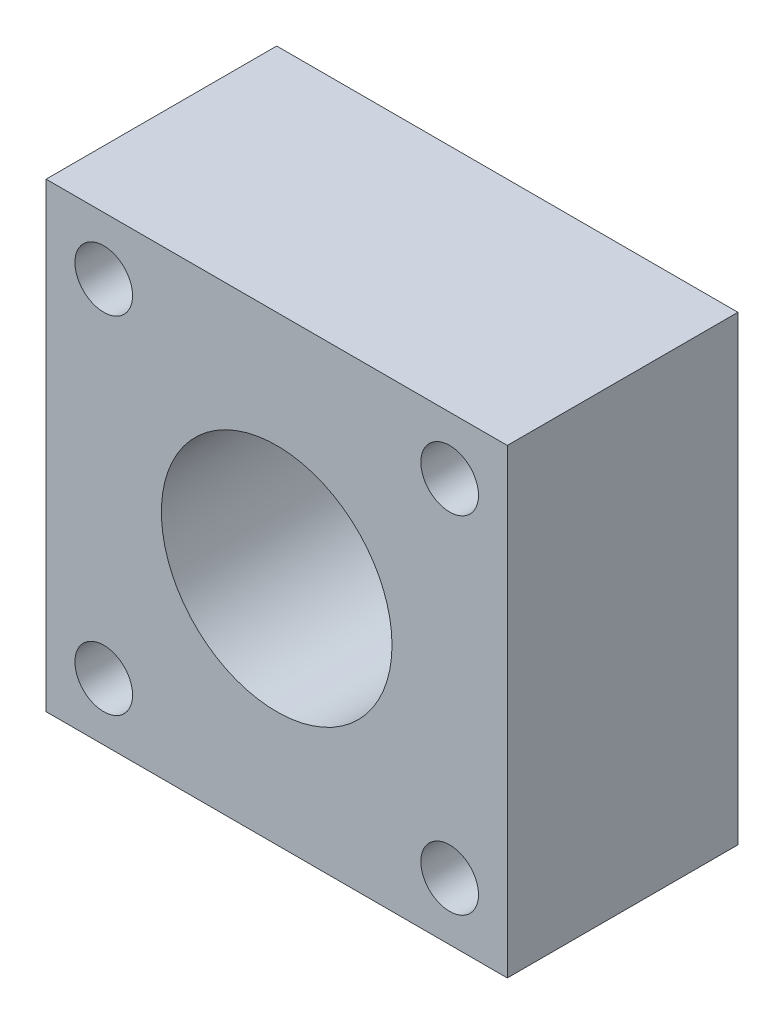
SolidWorks part; units mm, degrees
ref_plane "Front Plane" through (0, 0, 0) normal (0, 0, 1) x (1, 0, 0)
ref_plane "Top Plane" through (0, 0, 0) normal (0, 1, 0) x (1, 0, 0)
ref_plane "Right Plane" through (0, 0, 0) normal (1, 0, 0) x (0, 0, -1)
sketch "Sketch4" plane through (0, 0, 0) normal (0, 0, 1) x (1, 0, 0)
  line L1 (-25.4, 25.4) -> (25.4, 25.4)
  line L2 (-25.4, 25.4) -> (-25.4, -25.4)
  line L3 (-25.4, -25.4) -> (25.4, -25.4)
  line L4 (25.4, 25.4) -> (25.4, -25.4)
  line L5 (-25.4, 25.4) -> (25.4, -25.4) construction
  line L6 (-25.4, -25.4) -> (25.4, 25.4) construction
  point P0 (0, 0)
  dimension "D1" = 50.8
  dimension "D2" = 50.8
extrude "Boss-Extrude2" add sketch "Sketch4" along normal blind 25.4
sketch "Sketch5" plane through (0, 0, 25.4) normal (0, 0, 1) x (1, 0, 0)
  line L0 (25.4, -25.4) -> (25.4, 25.4) construction
  line L1 (25.4, 25.4) -> (-25.4, 25.4) construction
  line L2 (0, 27.1283) -> (0, -35.2779) construction
  circle A0 centre (19.05, 19.05) radius 3.175
  circle A1 centre (0, 0) radius 12.7
  circle A2 centre (-19.05, 19.05) radius 3.175
  circle A3 centre (19.05, -19.05) radius 3.175
  circle A4 centre (-19.05, -19.05) radius 3.175
  dimension "D1" = 6.35
  dimension "D4" = 25.4
  dimension "D2" = 6.35
  dimension "D3" = 6.35
  dimension "D5" = 2
  dimension "D6" = 2
extrude "Cut-Extrude5" cut sketch "Sketch5" against normal blind 25.4
